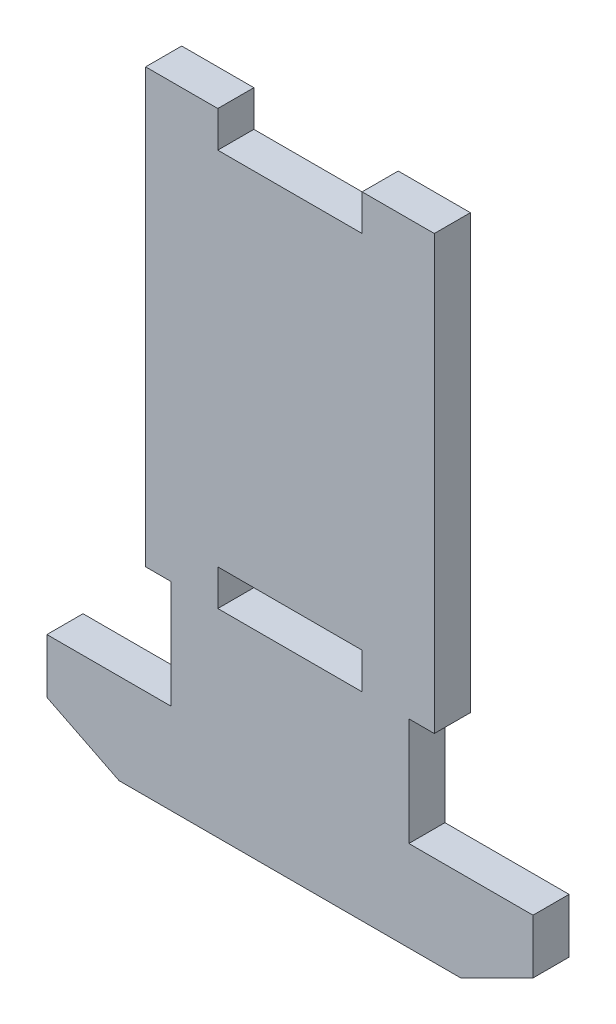
SolidWorks part; units mm, degrees
material "Acrylic (Medium-high impact)"
ref_plane "Front Plane" through (0, 0, 0) normal (0, 0, 1) x (1, 0, 0)
ref_plane "Top Plane" through (0, 0, 0) normal (0, 1, 0) x (1, 0, 0)
ref_plane "Right Plane" through (0, 0, 0) normal (1, 0, 0) x (0, 0, -1)
sketch "Sketch1" plane through (0, 0, 0) normal (0, 0, 1) x (1, 0, 0)
  line L0 (0, 0) -> (0, -4.9754) construction
  line L1 (-12.7, 19.05) -> (-6.35, 19.05)
  line L2 (-12.7, 19.05) -> (-12.7, -19.05)
  line L3 (-12.7, -19.05) -> (-6.35, -19.05)
  line L4 (12.7, 19.05) -> (12.7, -19.05)
  line L5 (0, 0) -> (12.7, -19.05) construction
  line L6 (-12.7, -19.05) -> (0, 0) construction
  line L7 (-3.0315, 0) -> (4.9857, 0) construction
  line L8 (6.35, 19.05) -> (12.7, 19.05)
  line L9 (6.35, -19.05) -> (6.35, -15.875)
  line L10 (-6.35, -15.875) -> (6.35, -15.875)
  line L11 (-6.35, -19.05) -> (-6.35, -15.875)
  line L12 (6.35, -19.05) -> (12.7, -19.05)
  line L17 (-6.35, 19.05) -> (-6.35, 15.875)
  line L18 (-6.35, 15.875) -> (6.35, 15.875)
  line L19 (6.35, 19.05) -> (6.35, 15.875)
  point P0 (0, 0)
  point P8 (12.7, 0)
  point P20 (0, 15.875)
  dimension "D5" = 12.7
  dimension "D1" = 25.4
  dimension "D2" = 38.1
  dimension "D3" = 3.175
  dimension "D4" = 6.35
extrude "Boss-Extrude1" add sketch "Sketch1" along normal blind 3.175
sketch "Sketch2" plane through (0, 0, 0) normal (0, 0, -1) x (-1, 0, 0)
  line L0 (12.7, 19.05) -> (12.7, -19.05) construction
  line L1 (-12.7, -19.05) -> (12.7, -19.05)
  line L2 (-12.7, -19.05) -> (-12.7, -36.5125)
  line L3 (-12.7, -36.5125) -> (12.7, -36.5125)
  line L4 (12.7, -19.05) -> (12.7, -36.5125)
  dimension "D1" = 17.4625
extrude "Boss-Extrude2" add sketch "Sketch2" against normal up to surface (3.175 mm away) contours L1 L4 L3 L2 up to face at (0, 0, 3.175)
sketch "Sketch4" plane through (0, 0, 0) normal (0, 0, -1) x (-1, 0, 0)
  line L0 (-12.7, -36.5125) -> (-12.7, 19.05) construction
  line L1 (-12.7, -19.05) -> (-10.462, -19.05)
  line L2 (-12.7, -19.05) -> (-12.7, -28.55)
  line L3 (-12.7, -28.55) -> (-10.462, -28.55)
  line L4 (-10.462, -19.05) -> (-10.462, -28.55)
  line L5 (-6.35, -19.05) -> (6.35, -19.05) construction
  dimension "D1" = 2.238
  dimension "D2" = 9.5
extrude "Cut-Extrude1" cut sketch "Sketch4" against normal up to next (3.175 mm away)
sketch "Sketch5" plane through (0, 0, 0) normal (0, 0, -1) x (-1, 0, 0)
  line L0 (-12.7, -36.5125) -> (12.7, -36.5125) construction
  line L1 (-12.7, -28.55) -> (-21.3843, -28.55)
  line L2 (-12.7, -28.55) -> (-12.7, -36.5125)
  line L3 (-12.7, -36.5125) -> (-21.3843, -36.5125)
  line L4 (-21.3843, -28.55) -> (-21.3843, -36.5125)
  dimension "D1" = 8.6843
extrude "Boss-Extrude3" add sketch "Sketch5" against normal up to surface (3.175 mm away) up to face at (3.8603, -5.0229, 3.175)
sketch "Sketch6" plane through (0, 0, 0) normal (0, 0, -1) x (-1, 0, 0)
  line L0 (-21.3843, -33.3375) -> (-15.0343, -36.5125)
  line L2 (-21.3843, -36.5125) -> (12.7, -36.5125) construction
  line L3 (-21.3843, -28.55) -> (-21.3843, -36.5125) construction
  line L4 (-21.3843, -36.5125) -> (-21.3843, -33.3375)
  line L5 (-21.3843, -36.5125) -> (-15.0343, -36.5125)
  dimension "D1" = 6.35
  dimension "D2" = 3.175
extrude "Cut-Extrude2" cut sketch "Sketch6" against normal up to next (3.175 mm away)
mirror "Mirror1" about plane through (0, 0, 0) normal (1, 0, 0) of "Cut-Extrude2", "Cut-Extrude1", "Boss-Extrude3"
sketch "Sketch7" [suppressed] plane through (0, 0, 0) normal (0, 0, -1) x (-1, 0, 0)
  line L0 (-6.35, -19.05) -> (6.35, -19.05) construction
  line L1 (-6.35, -15.875) -> (-6.35, -19.05) construction
  point P0 (-6.35, 15.875)
  point P1 (6.35, 15.875)
  point P3 (6.35, -15.875)
  point P5 (-6.35, -15.875)
  point P7 (-6.35, -19.05)
  point P9 (6.35, -19.05)
  point P14 (9.7, -19.05)
  point P16 (9.7, -28.55)
  point P18 (-9.7, -19.05)
  point P20 (-9.7, -28.55)
sketch "Sketch8" [suppressed] plane through (0, 0, 0) normal (0, 0, -1) x (-1, 0, 0)
  circle A0 centre (-6.35, 15.875) radius 0.635
  dimension "D1" = 1.27
extrude "Cut-Extrude3" [suppressed] cut sketch "Sketch8" against normal up to next
pattern_sketch "Sketch-Pattern1" [suppressed]
